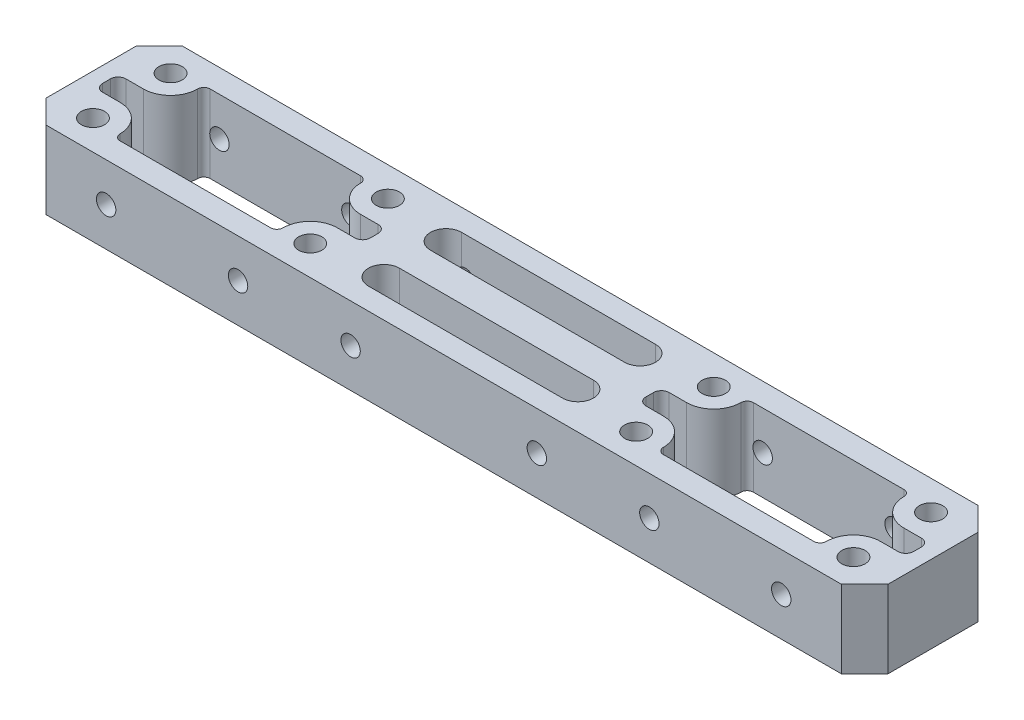
SolidWorks part; units mm, degrees
material "6061-T6 (SS)"
ref_plane "前视基准面" through (0, 0, 0) normal (0, 0, 1) x (1, 0, 0)
ref_plane "上视基准面" through (0, 0, 0) normal (0, 1, 0) x (1, 0, 0)
ref_plane "右视基准面" through (0, 0, 0) normal (1, 0, 0) x (0, 0, -1)
sketch "草图1" plane through (0, 0, 0) normal (0, 1, 0) x (1, 0, 0)
  line L2 (-19.25, 8.8) -> (19.25, 8.8)
  line L3 (-19.25, 8.8) -> (-19.25, -8.8)
  line L4 (-19.25, -8.8) -> (19.25, -8.8)
  line L5 (19.25, 8.8) -> (19.25, -8.8)
  line L6 (0, -8.8) -> (0, 8.8) construction
  line L7 (-19.25, 0) -> (19.25, 0) construction
  line L8 (-14, 5) -> (14, 5) construction
  line L9 (-14, 5) -> (-14, -5) construction
  line L10 (-14, -5) -> (14, -5) construction
  line L11 (14, 5) -> (14, -5) construction
  line L12 (0, -5) -> (0, 5) construction
  line L13 (-14, 0) -> (14, 0) construction
  circle A0 centre (-14, 5) radius 1.5
  circle A1 centre (-14, -5) radius 1.5
  circle A2 centre (14, -5) radius 1.5
  circle A3 centre (14, 5) radius 1.5
  point P0 (0, 0)
  point P2 (0, 0)
  dimension "D5" = 3
  dimension "D1" = 17.6
  dimension "D2" = 38.5
  dimension "D3" = 10
  dimension "D4" = 28
extrude "凸台-拉伸1" add sketch "草图1" along normal blind 10
cosmetic thread "装饰螺纹线1" parameters "D2"=4
cosmetic thread "装饰螺纹线2" parameters "D2"=4
cosmetic thread "装饰螺纹线3" parameters "D2"=4
cosmetic thread "装饰螺纹线4" parameters "D2"=4
cosmetic thread "装饰螺纹线5" parameters "D2"=4
cosmetic thread "装饰螺纹线6" parameters "D2"=4
cosmetic thread "装饰螺纹线7" parameters "D2"=4
cosmetic thread "装饰螺纹线8" parameters "D2"=4
sketch "草图2" plane through (0, 10, 0) normal (0, 1, 0) x (1, 0, 0)
  line L0 (0, 0) -> (0, -50000) construction
  line L1 (0, 0) -> (-50000, 0) construction
  line L2 (9.7, 5.8) -> (-9.7, 5.8)
  line L5 (19.25, 8.8) -> (-19.25, 8.8) construction
  line L6 (-14, 1.5) -> (-16.25, 1.5)
  line L7 (-17.25, 0.5) -> (-17.25, -0.5)
  line L8 (-19.25, 8.8) -> (-19.25, -8.8) construction
  line L9 (9.7, -5.8) -> (-9.7, -5.8)
  line L10 (-14, -1.5) -> (-16.25, -1.5)
  line L11 (14, -1.5) -> (16.25, -1.5)
  line L12 (17.25, 0.5) -> (17.25, -0.5)
  line L13 (14, 1.5) -> (16.25, 1.5)
  arc A0 (-9.7, 5.8) -> (-10.5, 5) centre (-9.7, 5) ccw
  arc A1 (-10.5, 5) -> (-14, 1.5) centre (-14, 5) cw
  arc A2 (-16.25, 1.5) -> (-17.25, 0.5) centre (-16.25, 0.5) ccw
  circle A3 centre (-14, 5) radius 1.5 construction
  circle A4 centre (-14, 5) radius 1.5 construction
  arc A5 (-9.7, -5.8) -> (-10.5, -5) centre (-9.7, -5) cw
  arc A6 (-10.5, -5) -> (-14, -1.5) centre (-14, -5) ccw
  arc A7 (-16.25, -1.5) -> (-17.25, -0.5) centre (-16.25, -0.5) cw
  arc A8 (9.7, -5.8) -> (10.5, -5) centre (9.7, -5) ccw
  arc A9 (10.5, -5) -> (14, -1.5) centre (14, -5) cw
  arc A10 (16.25, -1.5) -> (17.25, -0.5) centre (16.25, -0.5) ccw
  arc A11 (16.25, 1.5) -> (17.25, 0.5) centre (16.25, 0.5) cw
  arc A12 (10.5, 5) -> (14, 1.5) centre (14, 5) ccw
  arc A13 (9.7, 5.8) -> (10.5, 5) centre (9.7, 5) cw
  point P30 (-17.25, 0)
  point P33 (0, -5.8)
  point P46 (0, 5.8)
  dimension "D2" = 3.5
  dimension "1" = 1
  dimension "D1" = 3
  dimension "D3" = 2
extrude "切除-拉伸1" cut sketch "草图2" against normal through all
sketch "草图5" plane through (0, 10, 0) normal (0, 1, 0) x (1, 0, 0)
  line L1 (50.75, 8.8) -> (89.25, 8.8)
  line L2 (50.75, 8.8) -> (50.75, -8.8)
  line L3 (50.75, -8.8) -> (89.25, -8.8)
  line L4 (89.25, 8.8) -> (89.25, -8.8)
  line L5 (70, -8.8) -> (70, 8.8) construction
  line L6 (50.75, 0) -> (89.25, 0) construction
  line L8 (56, 5) -> (84, 5) construction
  line L9 (56, 5) -> (56, -5) construction
  line L10 (56, -5) -> (84, -5) construction
  line L11 (19.25, -8.8) -> (19.25, 8.8)
  line L12 (19.25, -8.8) -> (19.25, 8.8) construction
  line L13 (-19.25, 8.8) -> (-19.25, -8.8)
  line L14 (-19.25, -8.8) -> (19.25, -8.8)
  line L17 (-19.25, 8.8) -> (-19.25, -8.8) construction
  line L18 (-19.25, -8.8) -> (19.25, -8.8) construction
  line L19 (84, 5) -> (84, -5) construction
  line L20 (70, -5) -> (70, 5) construction
  line L21 (56, 0) -> (84, 0) construction
  line L25 (19.25, 8.8) -> (-19.25, 8.8)
  line L26 (19.25, 8.8) -> (-19.25, 8.8) construction
  circle A0 centre (56, 5) radius 1.5
  circle A1 centre (84, 5) radius 1.5
  circle A2 centre (84, -5) radius 1.5
  circle A3 centre (56, -5) radius 1.5
  point P0 (70, 0)
  point P6 (70, 0)
  dimension "D3" = 3
  dimension "D2" = 10
  dimension "38.5" = 38.5
  dimension "28" = 28
  dimension "D4" = 70
  dimension "D1" = 0
extrude "凸台-拉伸6" add sketch "草图5" against normal up to surface (10 mm away) separate body up to face at (0, 0, 0)
cosmetic thread "装饰螺纹线13" parameters "D2"=4
cosmetic thread "装饰螺纹线14" parameters "D2"=4
cosmetic thread "装饰螺纹线15" parameters "D2"=4
cosmetic thread "装饰螺纹线16" parameters "D2"=4
sketch "草图10" plane through (0, 10, 0) normal (0, 1, 0) x (1, 0, 0)
  line L1 (19.25, 8.8) -> (50.75, 8.8)
  line L2 (19.25, 8.8) -> (19.25, -8.8)
  line L3 (19.25, -8.8) -> (50.75, -8.8)
  line L4 (50.75, 8.8) -> (50.75, -8.8)
  line L5 (35, -8.8) -> (35, 8.8) construction
  line L6 (19.25, 0) -> (50.75, 0) construction
  point P236 (35, 0)
extrude "凸台-拉伸7" add sketch "草图10" against normal up to surface (10 mm away) up to face at (0, 0, 0)
sketch "草图11" plane through (0, 10, 0) normal (0, 1, 0) x (1, 0, 0)
  line L0 (35, -9) -> (35, -50009) construction
  line L1 (-19.25, -8.8) -> (89.25, -8.8) construction
  line L2 (16.25, 1.5) -> (14, 1.5) construction
  line L3 (17.25, -0.5) -> (17.25, 0.5) construction
  line L4 (14, -1.5) -> (16.25, -1.5) construction
  line L5 (-9.7, -5.8) -> (9.7, -5.8) construction
  line L6 (-16.25, -1.5) -> (-14, -1.5) construction
  line L7 (-17.25, 0.5) -> (-17.25, -0.5) construction
  line L8 (-14, 1.5) -> (-16.25, 1.5) construction
  line L9 (9.7, 5.8) -> (-9.7, 5.8) construction
  line L10 (16.25, 1.5) -> (14, 1.5)
  line L11 (17.25, -0.5) -> (17.25, 0.5)
  line L12 (14, -1.5) -> (16.25, -1.5)
  line L13 (-9.7, -5.8) -> (9.7, -5.8)
  line L14 (-16.25, -1.5) -> (-14, -1.5)
  line L15 (-17.25, 0.5) -> (-17.25, -0.5)
  line L16 (-14, 1.5) -> (-16.25, 1.5)
  line L17 (9.7, 5.8) -> (-9.7, 5.8)
  line L18 (53.75, 1.5) -> (56, 1.5)
  line L19 (52.75, -0.5) -> (52.75, 0.5)
  line L20 (56, -1.5) -> (53.75, -1.5)
  line L21 (79.7, -5.8) -> (60.3, -5.8)
  line L22 (86.25, -1.5) -> (84, -1.5)
  line L23 (87.25, 0.5) -> (87.25, -0.5)
  line L24 (84, 1.5) -> (86.25, 1.5)
  line L25 (60.3, 5.8) -> (79.7, 5.8)
  arc A0 (10.5, 5) -> (9.7, 5.8) centre (9.7, 5) ccw construction
  arc A1 (10.5, 5) -> (14, 1.5) centre (14, 5) ccw construction
  arc A2 (17.25, 0.5) -> (16.25, 1.5) centre (16.25, 0.5) ccw construction
  arc A3 (16.25, -1.5) -> (17.25, -0.5) centre (16.25, -0.5) ccw construction
  arc A4 (14, -1.5) -> (10.5, -5) centre (14, -5) ccw construction
  arc A5 (9.7, -5.8) -> (10.5, -5) centre (9.7, -5) ccw construction
  arc A6 (-10.5, -5) -> (-9.7, -5.8) centre (-9.7, -5) ccw construction
  arc A7 (-10.5, -5) -> (-14, -1.5) centre (-14, -5) ccw construction
  arc A8 (-17.25, -0.5) -> (-16.25, -1.5) centre (-16.25, -0.5) ccw construction
  arc A9 (-16.25, 1.5) -> (-17.25, 0.5) centre (-16.25, 0.5) ccw construction
  arc A10 (-14, 1.5) -> (-10.5, 5) centre (-14, 5) ccw construction
  arc A11 (-9.7, 5.8) -> (-10.5, 5) centre (-9.7, 5) ccw construction
  arc A12 (10.5, 5) -> (9.7, 5.8) centre (9.7, 5) ccw
  arc A13 (10.5, 5) -> (14, 1.5) centre (14, 5) ccw
  arc A14 (17.25, 0.5) -> (16.25, 1.5) centre (16.25, 0.5) ccw
  arc A15 (16.25, -1.5) -> (17.25, -0.5) centre (16.25, -0.5) ccw
  arc A16 (14, -1.5) -> (10.5, -5) centre (14, -5) ccw
  arc A17 (9.7, -5.8) -> (10.5, -5) centre (9.7, -5) ccw
  arc A18 (-10.5, -5) -> (-9.7, -5.8) centre (-9.7, -5) ccw
  arc A19 (-10.5, -5) -> (-14, -1.5) centre (-14, -5) ccw
  arc A20 (-17.25, -0.5) -> (-16.25, -1.5) centre (-16.25, -0.5) ccw
  arc A21 (-16.25, 1.5) -> (-17.25, 0.5) centre (-16.25, 0.5) ccw
  arc A22 (-14, 1.5) -> (-10.5, 5) centre (-14, 5) ccw
  arc A23 (-9.7, 5.8) -> (-10.5, 5) centre (-9.7, 5) ccw
  arc A24 (59.5, 5) -> (56, 1.5) centre (56, 5) cw
  arc A25 (52.75, 0.5) -> (53.75, 1.5) centre (53.75, 0.5) cw
  arc A26 (53.75, -1.5) -> (52.75, -0.5) centre (53.75, -0.5) cw
  arc A27 (56, -1.5) -> (59.5, -5) centre (56, -5) cw
  arc A28 (60.3, -5.8) -> (59.5, -5) centre (60.3, -5) cw
  arc A29 (80.5, -5) -> (79.7, -5.8) centre (79.7, -5) cw
  arc A30 (80.5, -5) -> (84, -1.5) centre (84, -5) cw
  arc A31 (87.25, -0.5) -> (86.25, -1.5) centre (86.25, -0.5) cw
  arc A32 (86.25, 1.5) -> (87.25, 0.5) centre (86.25, 0.5) cw
  arc A33 (84, 1.5) -> (80.5, 5) centre (84, 5) cw
  arc A34 (79.7, 5.8) -> (80.5, 5) centre (79.7, 5) cw
  arc A35 (59.5, 5) -> (60.3, 5.8) centre (60.3, 5) cw
  point P4 (35, -8.8)
extrude "切除-拉伸5" cut sketch "草图11" against normal through all
sketch "草图12" plane through (0, 10, 0) normal (0, 1, 0) x (1, 0, 0)
  line L0 (35, 9) -> (35, -49991) construction
  line L1 (89.25, 8.8) -> (-19.25, 8.8) construction
  line L2 (0, 0) -> (50000, 0) construction
  line L3 (22.5, 4) -> (47.5, 4) construction
  line L4 (22.5, 6) -> (47.5, 6)
  line L5 (22.5, 2) -> (47.5, 2)
  line L6 (22.5, -4) -> (47.5, -4) construction
  line L7 (22.5, -6) -> (47.5, -6)
  line L8 (22.5, -2) -> (47.5, -2)
  arc A0 (22.5, 6) -> (22.5, 2) centre (22.5, 4) ccw
  arc A1 (47.5, 2) -> (47.5, 6) centre (47.5, 4) ccw
  arc A2 (22.5, -6) -> (22.5, -2) centre (22.5, -4) cw
  arc A3 (47.5, -2) -> (47.5, -6) centre (47.5, -4) cw
  point P4 (35, 8.8)
  point P10 (35, 4)
  point P17 (35, -4)
  dimension "D2" = 4
  dimension "2.5" = 2
  dimension "D1" = 25
extrude "切除-拉伸6" cut sketch "草图12" against normal through all
chamfer "倒角1" distance 3 angle 45 4 edges at (89.25, 5, 8.8) (89.25, 5, -8.8) (-19.25, 5, -8.8) (-19.25, 5, 8.8)
sketch "草图13" plane through (0, 0, -8.8) normal (0, 0, -1) x (-1, 0, 0)
  line L0 (-60.3, 10) -> (-79.7, 10) construction
  line L2 (-60.3, 10) -> (-79.7, 10) construction
  line L3 (-79.7, 10) -> (-60.3, 10) construction
  line L4 (-79.7, 10) -> (-79.7, 0) construction
  line L5 (-60.3, 10) -> (-60.3, 0) construction
  line L6 (-79.7, 0) -> (-60.3, 0) construction
  line L7 (-60.3, 5) -> (-79.7, 5) construction
  line L8 (-70, 10) -> (-70, 0) construction
  line L9 (-86.25, 0) -> (16.25, 0) construction
  line L10 (-35, 10) -> (-35, -49990) construction
  line L11 (-79.7, 8) -> (-60.3, 8)
  line L12 (-79.7, 8) -> (-79.7, 2)
  line L13 (-79.7, 2) -> (-60.3, 2)
  line L14 (-60.3, 8) -> (-60.3, 2)
  line L15 (-70, 2) -> (-70, 8) construction
  line L16 (-79.7, 5) -> (-60.3, 5) construction
  line L17 (-86.25, 10) -> (16.25, 10) construction
  line L18 (9.7, 2) -> (-9.7, 2)
  line L19 (-9.7, 8) -> (-9.7, 2)
  line L20 (9.7, 8) -> (-9.7, 8)
  line L21 (9.7, 8) -> (9.7, 2)
  point P9 (-70, 5)
  point P17 (-35, 10)
  point P460 (-70, 5)
  dimension "D1" = 2
extrude "切除-拉伸7" [suppressed] cut sketch "草图13" against normal through all
fillet "圆角1" [suppressed] radius 2
sketch "草图14" plane through (0, 0, -8.8) normal (0, 0, -1) x (-1, 0, 0)
  line L0 (-35, 10) -> (-35, -49990) construction
  line L1 (-86.25, 10) -> (16.25, 10) construction
  line L2 (-89.25, 5) -> (-50089.25, 5) construction
  line L3 (-89.25, 0) -> (-89.25, 10) construction
  line L4 (-79.7, 10) -> (-60.3, 10) construction
  line L5 (-79.7, 10) -> (-60.3, 10) construction
  line L6 (-70, 10) -> (-70, -49990) construction
  circle A0 centre (-47, 5) radius 1.25
  circle A1 centre (-78.5, 5) radius 1.25
  circle A2 centre (-61.5, 5) radius 1.25
  circle A3 centre (-23, 5) radius 1.25
  circle A4 centre (-8.5, 5) radius 1.25
  circle A5 centre (8.5, 5) radius 1.25
  point P4 (-35, 10)
  point P9 (-89.25, 5)
  point P16 (-70, 10)
  dimension "D1" = 8.5
  dimension "3.2" = 2.5
  dimension "10" = 12
extrude "切除-拉伸8" cut sketch "草图14" against normal up to next
cosmetic thread "装饰螺纹线17" parameters "D2"=3
cosmetic thread "装饰螺纹线18" parameters "D2"=3
cosmetic thread "装饰螺纹线19" parameters "D2"=3
cosmetic thread "装饰螺纹线20" parameters "D2"=3
cosmetic thread "装饰螺纹线21" parameters "D2"=3
cosmetic thread "装饰螺纹线22" parameters "D2"=3
sketch "草图15" plane through (0, 0, 8.8) normal (0, 0, 1) x (1, 0, 0)
  circle A0 centre (-8.5, 5) radius 1.25 construction
  circle A1 centre (8.5, 5) radius 1.25 construction
  circle A2 centre (23, 5) radius 1.25 construction
  circle A3 centre (47, 5) radius 1.25 construction
  circle A4 centre (61.5, 5) radius 1.25 construction
  circle A5 centre (78.5, 5) radius 1.25 construction
  circle A6 centre (-8.5, 5) radius 1.25
  circle A7 centre (8.5, 5) radius 1.25
  circle A8 centre (23, 5) radius 1.25
  circle A9 centre (47, 5) radius 1.25
  circle A10 centre (61.5, 5) radius 1.25
  circle A11 centre (78.5, 5) radius 1.25
extrude "切除-拉伸9" cut sketch "草图15" against normal up to next
cosmetic thread "装饰螺纹线23" parameters "D2"=3
cosmetic thread "装饰螺纹线24" parameters "D2"=3
cosmetic thread "装饰螺纹线25" parameters "D2"=3
cosmetic thread "装饰螺纹线26" parameters "D2"=3
cosmetic thread "装饰螺纹线27" parameters "D2"=3
cosmetic thread "装饰螺纹线28" parameters "D2"=3
